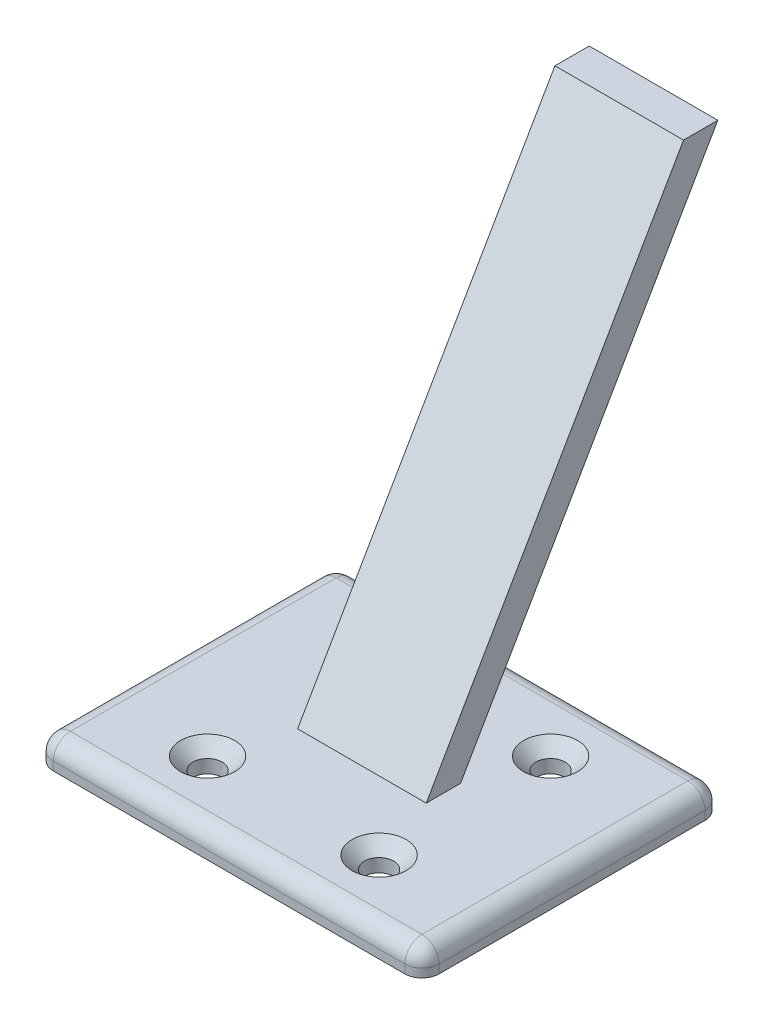
SolidWorks part; units mm, degrees
ref_plane "Front Plane" through (0, 0, 0) normal (0, 0, 1) x (1, 0, 0)
ref_plane "Top Plane" through (0, 0, 0) normal (0, 1, 0) x (1, 0, 0)
ref_plane "Right Plane" through (0, 0, 0) normal (1, 0, 0) x (0, 0, -1)
sketch "Sketch1" plane through (0, 0, 0) normal (0, 1, 0) x (1, 0, 0)
  line L1 (22.5, 17.5) -> (-22.5, 17.5)
  line L2 (22.5, 17.5) -> (22.5, -17.5)
  line L3 (22.5, -17.5) -> (-22.5, -17.5)
  line L4 (-22.5, 17.5) -> (-22.5, -17.5)
  line L5 (22.5, 17.5) -> (-22.5, -17.5) construction
  line L6 (22.5, -17.5) -> (-22.5, 17.5) construction
  point P0 (0, 0)
  dimension "D1" = 35
  dimension "D2" = 45
extrude "Boss-Extrude1" add sketch "Sketch1" along normal blind 3
sketch "Sketch2" plane through (0, 3, 0) normal (0, 1, 0) x (1, 0, 0)
  line L0 (-22.5, -17.5) -> (22.5, -17.5) construction
  line L1 (-22.5, 17.5) -> (-22.5, -17.5) construction
  line L2 (0, 17.5) -> (0, -17.5) construction
  line L3 (22.5, 17.5) -> (-22.5, 17.5) construction
  line L4 (-22.5, 0) -> (22.5, 0) construction
  line L5 (22.5, -17.5) -> (22.5, 17.5) construction
  point P0 (-10, -10)
  point P13 (10, -10)
  point P14 (10, 10)
  point P15 (-10, 10)
  dimension "D1" = 7.5
  dimension "D2" = 12.5
hole_wizard "CSK for M3 Flat Head Machine Screw2" positions "Sketch6" profile "Sketch5" countersink size "M3" standard "ANSI Metric" end condition up to next
sketch "Sketch6" plane through (0, 3, 0) normal (0, 1, 0) x (1, 0, 0)
  point P0 (10, 10)
  point P3 (-10, 10)
  point P6 (-10, -10)
  point P9 (10, -10)
sketch "Sketch5" plane through (10, 3, -10) normal (1, 0, 0) x (0, 0, 1)
  line L0 (0, 0) -> (0, 3)
  line L1 (0, 3) -> (1.7, 3)
  line L2 (1.7, 3) -> (1.7, 1.45)
  line L3 (1.7, 1.45) -> (3.15, 0)
  line L5 (3.15, 0) -> (0, 0)
  line L6 (-1.7, 1.45) -> (-3.15, 0) construction
  line L11 (0, -6.35) -> (0, 107.95) construction
  dimension "Thru Hole Dia." = 3.4
  dimension "Thru Hole Depth" = 3
  dimension "Near C'Sink Dia." = 6.3
  dimension "Near C'Sink Angle" = 90
sketch "Sketch11" plane through (22.5, 0, 0) normal (1, 0, 0) x (0, 0, -1)
  line L0 (0, 3) -> (17.3912, 33.1225) construction
  line L1 (17.5, 3) -> (-17.5, 3) construction
  dimension "D1" = 60
sketch "Sketch7" plane through (0, 3, 0) normal (0, 1, 0) x (1, 0, 0)
  line L1 (-7.5, -2) -> (7.5, -2)
  line L2 (-7.5, -2) -> (-7.5, 2)
  line L3 (-7.5, 2) -> (7.5, 2)
  line L4 (7.5, -2) -> (7.5, 2)
  line L5 (-7.5, -2) -> (7.5, 2) construction
  line L6 (-7.5, 2) -> (7.5, -2) construction
  point P0 (0, 0)
  dimension "D1" = 4
  dimension "D2" = 15
extrude "Boss-Extrude2" add sketch "Sketch7" along direction (0, 0.866, -0.5) on the side of the normal blind 60 from offset 0
fillet "Fillet1" radius 2 8 edges at (-22.5, 3, 0) (0, 3, -17.5) (22.5, 3, 0) (0, 3, 17.5) (-22.5, 1.5, -17.5) (22.5, 1.5, -17.5) (-22.5, 1.5, 17.5) (22.5, 1.5, 17.5)
